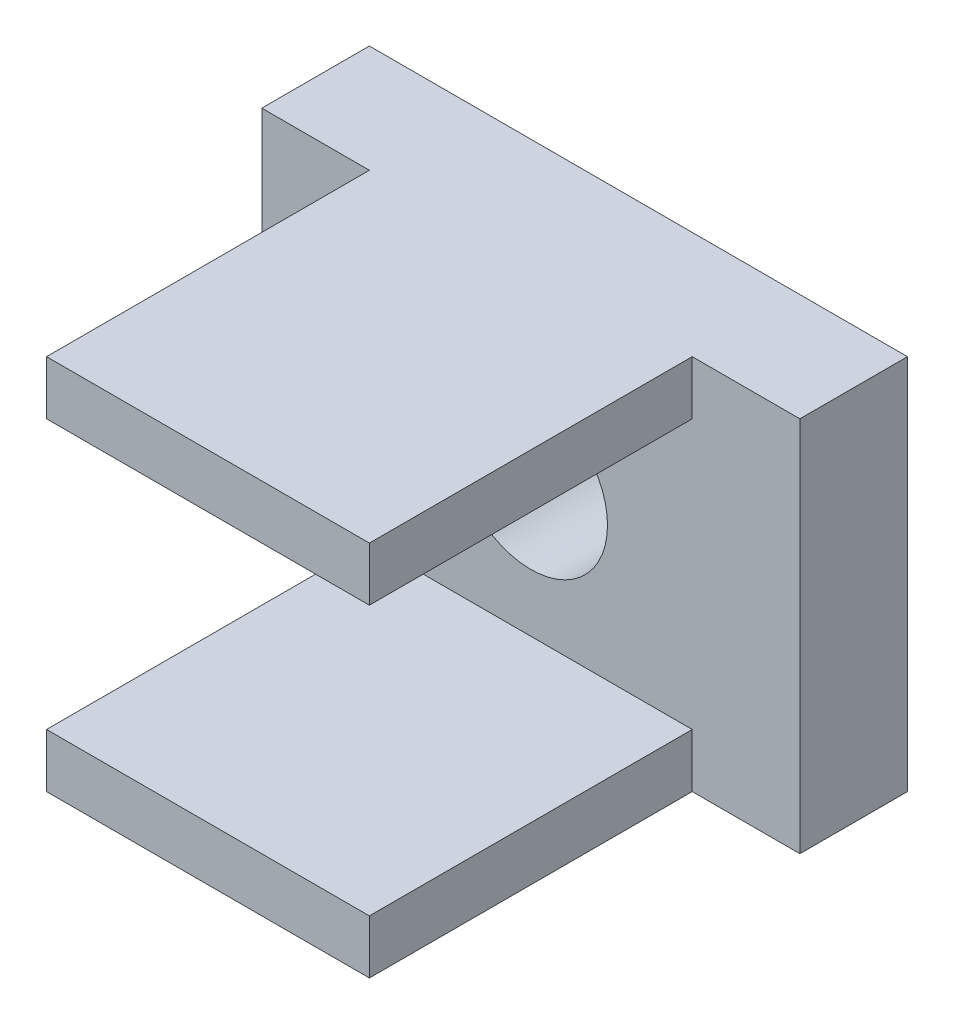
SolidWorks part; units mm, degrees
ref_plane "Front Plane" through (0, 0, 0) normal (0, 0, 1) x (1, 0, 0)
ref_plane "Top Plane" through (0, 0, 0) normal (0, 1, 0) x (1, 0, 0)
ref_plane "Right Plane" through (0, 0, 0) normal (1, 0, 0) x (0, 0, -1)
sketch "Sketch2" plane through (0, 0, 0) normal (0, 0, 1) x (1, 0, 0)
  line L1 (5, 3.5) -> (-5, 3.5)
  line L2 (5, 3.5) -> (5, -3.5)
  line L3 (5, -3.5) -> (-5, -3.5)
  line L4 (-5, 3.5) -> (-5, -3.5)
  line L5 (5, 3.5) -> (-5, -3.5) construction
  line L6 (5, -3.5) -> (-5, 3.5) construction
  point P0 (0, 0)
  dimension "D1" = 10
  dimension "D2" = 7
extrude "Boss-Extrude1" add sketch "Sketch2" along normal mid plane 2
sketch "Sketch3" plane through (0, 0, 1) normal (0, 0, 1) x (1, 0, 0)
  circle A0 centre (0, 0) radius 1.425
  dimension "D1" = 2.85
extrude "Cut-Extrude1" cut sketch "Sketch3" against normal through all
sketch "Sketch4" plane through (0, 0, 1) normal (0, 0, 1) x (1, 0, 0)
  line L0 (5, 3.5) -> (-5, 3.5) construction
  line L1 (-3, 3.5) -> (3, 3.5)
  line L2 (-3, 3.5) -> (-3, 2.5)
  line L3 (-3, 2.5) -> (3, 2.5)
  line L4 (3, 3.5) -> (3, 2.5)
  line L5 (-5, -3.5) -> (5, -3.5) construction
  line L6 (3, -3.5) -> (-3, -3.5)
  line L7 (3, -3.5) -> (3, -2.5)
  line L8 (3, -2.5) -> (-3, -2.5)
  line L9 (-3, -3.5) -> (-3, -2.5)
  line L10 (0, -5.636) -> (0, 7.3967) construction
  dimension "D1" = 1
  dimension "D2" = 1
  dimension "D3" = 6
  dimension "D4" = 6
extrude "Boss-Extrude2" add sketch "Sketch4" along normal blind 6
